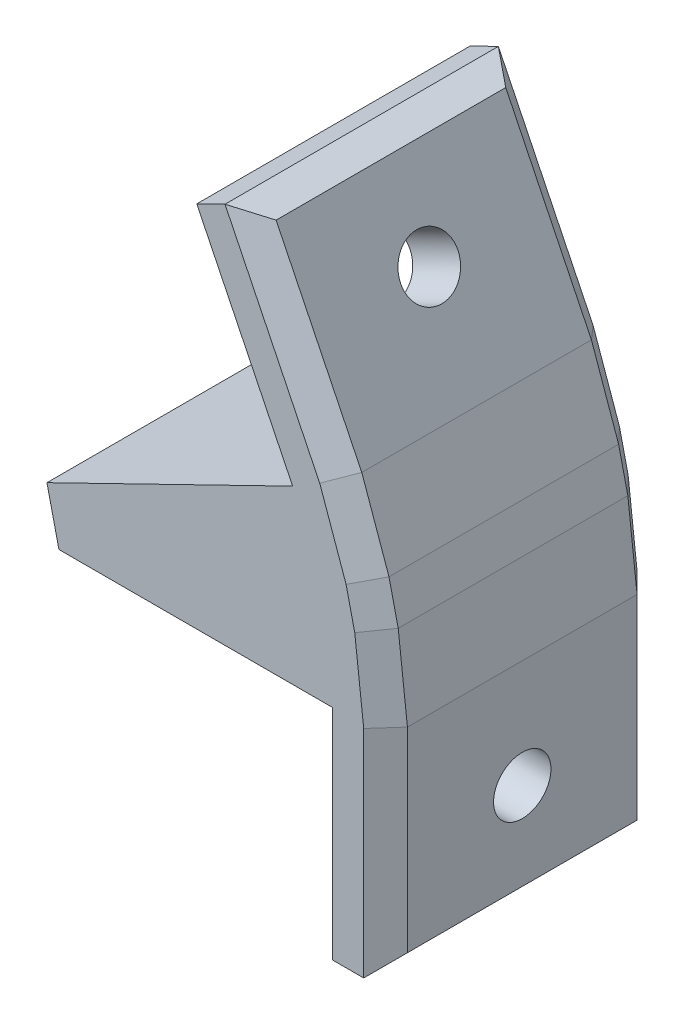
SolidWorks part; units mm, degrees
ref_plane "Plan de face" through (0, 0, 0) normal (0, 0, 1) x (1, 0, 0)
ref_plane "Plan de dessus" through (0, 0, 0) normal (0, 1, 0) x (1, 0, 0)
ref_plane "Plan de droite" through (0, 0, 0) normal (1, 0, 0) x (0, 0, -1)
sketch "Esquisse1" plane through (0, 0, 0) normal (0, 0, 1) x (1, 0, 0)
  line L0 (0, 0) -> (20, 0)
  line L1 (20, 0) -> (17.9759, 8.7674)
  line L2 (17.9759, 8.7674) -> (0, 0)
  dimension "D1" = 20
  dimension "D2" = 20
  dimension "D3" = 26
extrude "Boss.-Extru.1" add sketch "Esquisse1" along normal blind 20
sketch "Esquisse2" plane through (0, 0, 0) normal (-0.4384, 0.8988, 0) x (0.8988, 0.4384, 0)
  line L1 (0, -20) -> (20, -20)
  line L2 (0, -20) -> (0, 0)
  line L3 (0, 0) -> (20, 0)
  line L4 (20, -20) -> (20, 0)
extrude "Boss.-Extru.2" add sketch "Esquisse2" along normal blind 2
sketch "Esquisse3" plane through (0, 0, 0) normal (0, -1, 0) x (1, 0, 0)
  line L1 (0, 20) -> (20, 20)
  line L2 (0, 20) -> (0, 0)
  line L3 (0, 0) -> (20, 0)
  line L4 (20, 20) -> (20, 0)
extrude "Boss.-Extru.3" add sketch "Esquisse3" along normal blind 2
sketch "Esquisse4" plane through (18.9879, 4.3837, 0) normal (0.9744, 0.225, 0) x (0, 0, -1)
  line L1 (-20, 4.499) -> (0, 4.499)
  line L2 (-20, 4.499) -> (-20, -4.499)
  line L3 (-20, -4.499) -> (0, -4.499)
  line L4 (0, 4.499) -> (0, -4.499)
extrude "Boss.-Extru.4" add sketch "Esquisse4" along normal blind 4
sketch "Esquisse5" plane through (0, 0, 20) normal (0, 0, 1) x (1, 0, 0)
  line L0 (17.0991, 10.565) -> (10.0852, 24.9457)
  line L1 (10.0852, 24.9457) -> (13.5882, 26.6543)
  line L2 (13.5882, 26.6543) -> (21.8734, 9.6672)
  line L3 (21.8734, 9.6672) -> (17.9759, 8.7674)
  line L4 (17.9759, 8.7674) -> (17.0991, 10.565)
  line L5 (20, 0) -> (20, -2)
  line L6 (20, -2) -> (20, -18)
  line L7 (20, -18) -> (23.8975, -18)
  line L8 (23.8975, -18) -> (23.8975, 0.8998)
  line L9 (23.8975, 0.8998) -> (20, 0)
  dimension "D1" = 16
  dimension "D2" = 16
extrude "Boss.-Extru.5" add sketch "Esquisse5" against normal blind 20
chamfer "Chanfrein1" distance 3 distance2 3 2 edges at (23.8975, 0.8998, 10) (21.8734, 9.6672, 10)
chamfer "Chanfrein2" distance 1.6 angle 45 12 edges at (23.8975, -18, 10) (23.8975, -10.0501, 0) (23.8975, -10.0501, 20) (23.5601, 0.8614, 0) (22.8854, 5.2835, 0) (21.5532, 9.5539, 0) (17.0732, 19.5089, 20) (17.0732, 19.5089, 0) (13.5882, 26.6543, 10) (21.5532, 9.5539, 20) (22.8854, 5.2835, 20) (23.5601, 0.8614, 20)
sketch "Esquisse7" plane through (17.9759, 8.7674, 0) normal (-0.8988, -0.4384, 0) x (0, 0, 1)
  line L0 (0, 18) -> (20, 18) construction
  line L1 (20, 18) -> (20, 2) construction
  circle A0 centre (10, 10) radius 2.1
  dimension "D1" = 4.2
  dimension "D2" = 8
  dimension "D3" = 10
extrude "Enlèv. mat.-Extru.1" cut sketch "Esquisse7" against normal through all
sketch "Esquisse8" plane through (20, 0, 0) normal (-1, 0, 0) x (0, 0, 1)
  line L0 (0, -2) -> (0, -18) construction
  line L1 (0, -18) -> (20, -18) construction
  circle A0 centre (10, -10) radius 2.1
  dimension "D1" = 4.2
  dimension "D2" = 10
  dimension "D3" = 8
extrude "Enlèv. mat.-Extru.2" cut sketch "Esquisse8" against normal through all
sketch "Esquisse9" plane through (0, 0, 20) normal (0, 0, 1) x (1, 0, 0)
  line L0 (-0.8767, 1.7976) -> (0, 0)
  line L1 (0, 0) -> (0, -2)
  line L2 (0, -2) -> (-0.8767, 1.7976)
extrude "Boss.-Extru.6" add sketch "Esquisse9" against normal blind 20
